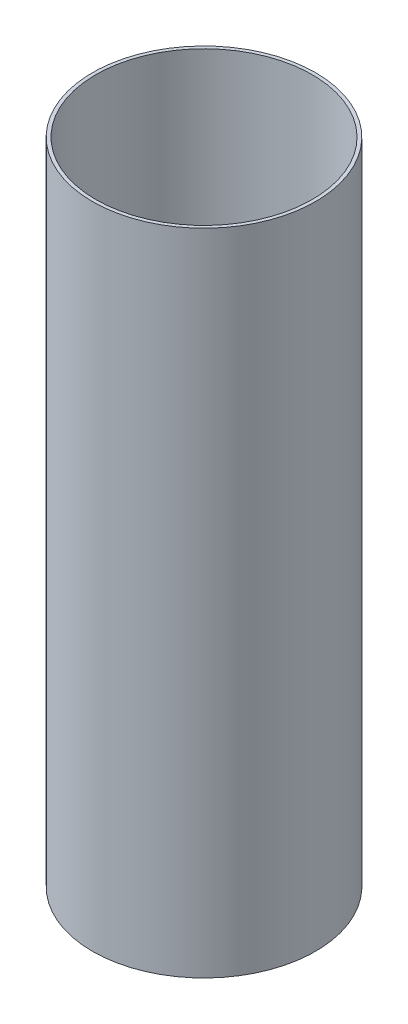
SolidWorks part; units mm, degrees
ref_plane "Front Plane" through (0, 0, 0) normal (0, 0, 1) x (1, 0, 0)
ref_plane "Top Plane" through (0, 0, 0) normal (0, 1, 0) x (1, 0, 0)
ref_plane "Right Plane" through (0, 0, 0) normal (1, 0, 0) x (0, 0, -1)
sketch "Sketch1" plane through (0, 0, 0) normal (0, 1, 0) x (1, 0, 0)
  circle A0 centre (0, 0) radius 101.6
  circle A1 centre (0, 0) radius 104.775
extrude "Boss-Extrude1" add sketch "Sketch1" along normal blind 609.6
